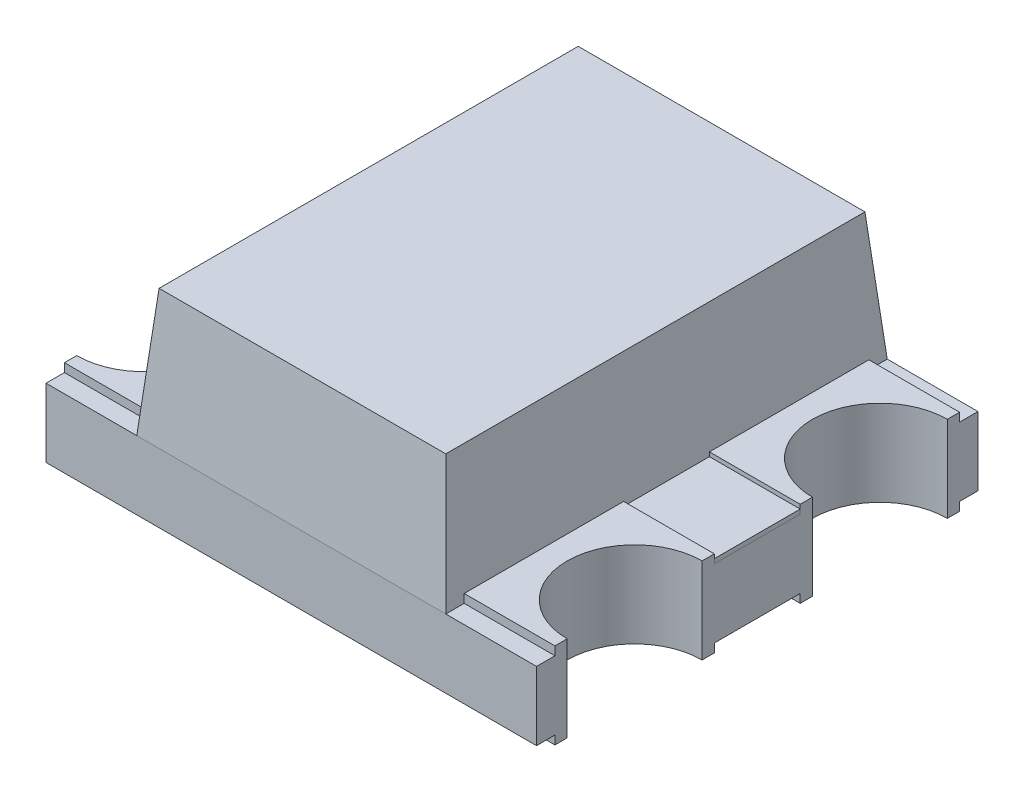
SolidWorks part; units mm, degrees
ref_plane "Front" through (0, 0, 0) normal (0, 0, 1) x (1, 0, 0)
ref_plane "Top" through (0, 0, 0) normal (0, 1, 0) x (1, 0, 0)
ref_plane "Right" through (0, 0, 0) normal (1, 0, 0) x (0, 0, -1)
sketch "Эскиз1" plane through (0, 0, 0) normal (0, 1, 0) x (1, 0, 0)
  line L1 (-1, 0.9) -> (1, 0.9)
  line L2 (-1, 0.9) -> (-1, -0.9)
  line L3 (-1, -0.9) -> (1, -0.9)
  line L4 (1, 0.9) -> (1, -0.9)
  line L5 (-1, 0.9) -> (1, -0.9) construction
  line L6 (-1, -0.9) -> (1, 0.9) construction
  point P0 (0, 0)
  dimension "D1" = 1.8
  dimension "D2" = 2
extrude "Бобышка-Вытянуть1" add sketch "Эскиз1" along normal blind 0.28
sketch "Эскиз2" plane through (0, 0.28, 0) normal (0, 1, 0) x (1, 0, 0)
  line L0 (-1, 0) -> (1, 0) construction
  line L1 (-1, 0.9) -> (-1, -0.9) construction
  line L2 (1, -0.9) -> (1, 0.9) construction
  line L3 (0, 0.9) -> (0, -0.9) construction
  line L4 (-1, -0.9) -> (1, -0.9) construction
  line L5 (-1, -0.9) -> (1, -0.9) construction
  circle A0 centre (1, 0.5) radius 0.275
  circle A1 centre (1, -0.5) radius 0.275
  circle A2 centre (-1, 0.5) radius 0.275
  circle A3 centre (-1, -0.5) radius 0.275
  point P15 (0, 0)
  point P19 (0, 0)
  dimension "D1" = 0.55
  dimension "D2" = 0.4
sketch "Эскиз7" plane through (0, 0, 0) normal (0, -1, 0) x (1, 0, 0)
  line L0 (-1, -0.9) -> (-1, 0.9) construction
  line L1 (0.3637, 0) -> (-0.1819, 0.315)
  line L2 (-0.1819, 0.315) -> (-0.1819, -0.315)
  line L3 (-0.1819, -0.315) -> (0.3637, 0)
  circle A0 centre (0, 0) radius 0.1819 construction
  point P7 (0, 0)
  dimension "D1" = 0.63
extrude "Бобышка-Вытянуть3" add sketch "Эскиз7" along normal blind 0.018
sketch "Эскиз8" plane through (0, 0, 0) normal (0, -1, 0) x (-1, 0, 0)
  line L0 (-1, -0.825) -> (-0.47, -0.825)
  line L1 (-1, -0.9) -> (-1, 0.9) construction
  line L2 (-0.47, -0.825) -> (-0.47, -0.175)
  line L3 (-0.47, -0.175) -> (-1, -0.175)
  line L4 (-1, -0.175) -> (-1, -0.825)
  line L6 (0, -0.9) -> (0, 0.9) construction
  line L7 (1, 0) -> (-1, 0) construction
  line L8 (0.47, -0.175) -> (1, -0.175)
  line L9 (0.47, -0.825) -> (0.47, -0.175)
  line L10 (1, -0.825) -> (0.47, -0.825)
  line L11 (1, -0.175) -> (1, -0.825)
  line L12 (-0.47, 0.175) -> (-1, 0.175)
  line L13 (-0.47, 0.825) -> (-0.47, 0.175)
  line L14 (-1, 0.825) -> (-0.47, 0.825)
  line L15 (-1, 0.175) -> (-1, 0.825)
  line L16 (0.47, 0.825) -> (0.47, 0.175)
  line L17 (1, 0.825) -> (0.47, 0.825)
  line L18 (1, 0.175) -> (1, 0.825)
  line L19 (0.47, 0.175) -> (1, 0.175)
  point P6 (-1, -0.5)
  dimension "D1" = 0.35
  dimension "D2" = 0.53
extrude "Бобышка-Вытянуть4" add sketch "Эскиз8" along normal blind 0.035
sketch "Эскиз9" plane through (0, 0.28, 0) normal (0, 1, 0) x (1, 0, 0)
  line L0 (1, -0.175) -> (1, -0.825) construction
  line L1 (1, -0.825) -> (0.47, -0.825) construction
  line L3 (0.47, -0.175) -> (1, -0.175) construction
  line L5 (0.47, 0.825) -> (1, 0.825) construction
  line L6 (1, 0.825) -> (1, 0.175) construction
  line L7 (1, 0.175) -> (0.47, 0.175) construction
  line L9 (-0.47, -0.825) -> (-1, -0.825) construction
  line L10 (-1, -0.825) -> (-1, -0.175) construction
  line L11 (-1, -0.175) -> (-0.47, -0.175) construction
  line L12 (-1, 0.825) -> (-0.47, 0.825) construction
  line L14 (-0.47, 0.175) -> (-1, 0.175) construction
  line L15 (-1, 0.175) -> (-1, 0.825) construction
  line L16 (1, -0.175) -> (1, -0.825)
  line L17 (1, -0.825) -> (0.63, -0.825)
  line L19 (0.63, -0.175) -> (1, -0.175)
  line L21 (0.63, 0.825) -> (1, 0.825)
  line L22 (1, 0.825) -> (1, 0.175)
  line L23 (1, 0.175) -> (0.63, 0.175)
  line L25 (-0.63, -0.825) -> (-1, -0.825)
  line L26 (-1, -0.825) -> (-1, -0.175)
  line L27 (-1, -0.175) -> (-0.63, -0.175)
  line L28 (-1, 0.825) -> (-0.63, 0.825)
  line L30 (-0.63, 0.175) -> (-1, 0.175)
  line L31 (-1, 0.175) -> (-1, 0.825)
  line L32 (-0.63, 0.825) -> (-0.63, 0.175)
  line L33 (1, 0.9) -> (-1, 0.9) construction
  line L34 (-1, -0.9) -> (1, -0.9) construction
  line L35 (0, 0.9) -> (0, -0.9) construction
  line L36 (0.63, 0.825) -> (0.63, 0.175)
  line L37 (-0.63, -0.175) -> (-0.63, -0.825)
  line L38 (0.63, -0.175) -> (0.63, -0.825)
  dimension "D1" = 1.26
extrude "Бобышка-Вытянуть5" add sketch "Эскиз9" along normal blind 0.035
extrude "Вырез-Вытянуть2" cut sketch "Эскиз2" against normal through all both and the other way through all
sketch "Эскиз13" plane through (0, 0.28, 0) normal (0, 1, 0) x (1, 0, 0)
  line L0 (-1, -0.9) -> (1, -0.9) construction
  line L1 (-0.63, 0.9) -> (0.63, 0.9)
  line L2 (-0.63, 0.9) -> (-0.63, -0.9)
  line L3 (-0.63, -0.9) -> (0.63, -0.9)
  line L4 (0.63, 0.9) -> (0.63, -0.9)
  line L5 (-0.63, 0.9) -> (0.63, -0.9) construction
  line L6 (-0.63, -0.9) -> (0.63, 0.9) construction
  point P0 (0, 0)
  dimension "D1" = 1.26
extrude "Бобышка-Вытянуть9" add sketch "Эскиз13" along normal blind 0.52 draft 5 separate body
sketch "Эскиз14" plane through (0, 0.28, 0) normal (0, 1, 0) x (1, 0, 0)
  line L1 (0.63, 0.175) -> (1, 0.175)
  line L2 (0.63, 0.175) -> (0.63, -0.175)
  line L3 (0.63, -0.175) -> (1, -0.175)
  line L4 (1, 0.175) -> (1, -0.175)
extrude "Бобышка-Вытянуть10" add sketch "Эскиз14" along normal blind 0.018 separate body
sketch "Эскиз15" plane through (0, 0.28, 0) normal (0, 1, 0) x (1, 0, 0)
  line L0 (-0.63, 0.4191) -> (-0.4748, 0.4191)
  line L1 (-0.63, 0.175) -> (-0.63, 0.825) construction
  line L2 (-0.4454, 0.4319) -> (-0.1966, 0.7017)
  line L3 (-0.1672, 0.7146) -> (0.458, 0.7146)
  line L4 (0.498, 0.6746) -> (0.498, 0.1248)
  line L5 (0.458, 0.0848) -> (-0.4173, 0.0848)
  line L6 (-0.4573, 0.1248) -> (-0.4573, 0.135)
  line L7 (-0.4973, 0.175) -> (-0.63, 0.175)
  line L8 (-0.63, 0.175) -> (-0.63, 0.4191)
  line L9 (-0.63, -0.175) -> (-0.3333, -0.175)
  line L10 (-0.2933, -0.215) -> (-0.2933, -0.2244)
  line L11 (-0.2533, -0.2644) -> (-0.172, -0.2644)
  line L12 (-0.132, -0.2244) -> (-0.132, -0.215)
  line L13 (-0.092, -0.175) -> (0.458, -0.175)
  line L14 (0.498, -0.215) -> (0.498, -0.785)
  line L15 (0.458, -0.825) -> (-0.63, -0.825)
  line L16 (-0.63, -0.825) -> (-0.63, -0.175)
  arc A0 (-0.132, -0.215) -> (-0.092, -0.175) centre (-0.092, -0.215) cw
  arc A1 (-0.3333, -0.175) -> (-0.2933, -0.215) centre (-0.3333, -0.215) cw
  arc A2 (-0.4573, 0.135) -> (-0.4973, 0.175) centre (-0.4973, 0.135) ccw
  arc A3 (-0.4573, 0.1248) -> (-0.4173, 0.0848) centre (-0.4173, 0.1248) ccw
  arc A4 (0.458, 0.0848) -> (0.498, 0.1248) centre (0.458, 0.1248) ccw
  arc A5 (0.498, 0.6746) -> (0.458, 0.7146) centre (0.458, 0.6746) ccw
  arc A6 (-0.1672, 0.7146) -> (-0.1966, 0.7017) centre (-0.1672, 0.6746) ccw
  arc A7 (-0.4454, 0.4319) -> (-0.4748, 0.4191) centre (-0.4748, 0.4591) cw
  arc A8 (0.498, -0.785) -> (0.458, -0.825) centre (0.458, -0.785) cw
  arc A9 (0.458, -0.175) -> (0.498, -0.215) centre (0.458, -0.215) cw
  arc A10 (-0.172, -0.2644) -> (-0.132, -0.2244) centre (-0.172, -0.2244) ccw
  arc A11 (-0.2933, -0.2244) -> (-0.2533, -0.2644) centre (-0.2533, -0.2244) ccw
  dimension "D1" = 0.04
  dimension "D2" = 0.04
extrude "Бобышка-Вытянуть11" add sketch "Эскиз15" along normal blind 0.035 separate body
sketch "Эскиз16" plane through (0, 0.315, 0) normal (0, 1, 0) x (1, 0, 0)
  line L1 (-0.065, 0.4624) -> (0.4293, 0.4624)
  line L2 (-0.065, 0.4624) -> (-0.065, 0.1567)
  line L3 (-0.065, 0.1567) -> (0.4293, 0.1567)
  line L4 (0.4293, 0.4624) -> (0.4293, 0.1567)
  line L5 (-0.5414, -0.2255) -> (-0.4204, -0.2255)
  line L6 (-0.5414, -0.2255) -> (-0.5414, -0.3732)
  line L7 (-0.5414, -0.3732) -> (-0.4204, -0.3732)
  line L8 (-0.4204, -0.2255) -> (-0.4204, -0.3732)
  line L9 (0.1107, -0.2232) -> (0.2165, -0.2232)
  line L10 (0.1107, -0.2232) -> (0.1107, -0.3761)
  line L11 (0.1107, -0.3761) -> (0.2165, -0.3761)
  line L12 (0.2165, -0.2232) -> (0.2165, -0.3761)
  line L13 (-0.3151, -0.5732) -> (-0.0629, -0.5732)
  line L14 (-0.3151, -0.5732) -> (-0.3151, -0.7056)
  line L15 (-0.3151, -0.7056) -> (-0.0629, -0.7056)
  line L16 (-0.0629, -0.5732) -> (-0.0629, -0.7056)
extrude "Бобышка-Вытянуть12" add sketch "Эскиз16" along normal blind 0.1 separate body
